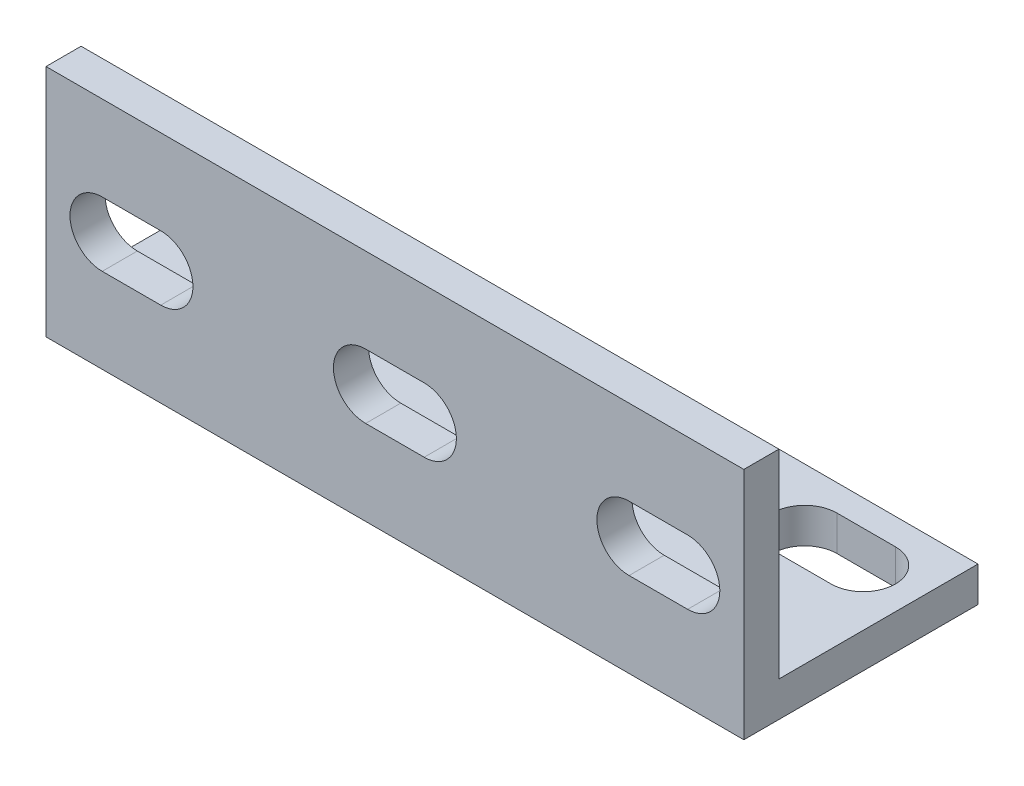
SolidWorks part; units mm, degrees
ref_plane "Front Plane" through (0, 0, 0) normal (0, 0, 1) x (1, 0, 0)
ref_plane "Top Plane" through (0, 0, 0) normal (0, 1, 0) x (1, 0, 0)
ref_plane "Right Plane" through (0, 0, 0) normal (1, 0, 0) x (0, 0, -1)
sketch "Sketch1" plane through (0, 0, 0) normal (1, 0, 0) x (0, 0, -1)
  line L0 (0, 20) -> (0, 0)
  line L1 (0, 0) -> (20, 0)
  line L2 (20, 0) -> (20, 3)
  line L3 (20, 3) -> (3, 3)
  line L4 (3, 3) -> (3, 20)
  line L5 (3, 20) -> (0, 20)
  dimension "D1" = 20
  dimension "D2" = 20
  dimension "D3" = 3
  dimension "D4" = 3
extrude "Boss-Extrude1" add sketch "Sketch1" against normal blind 59.6
sketch "Sketch2" plane through (0, 0, -3) normal (0, 0, -1) x (-1, 0, 0)
  line L0 (29.8, 20) -> (29.8, 3) construction
  line L1 (59.6, 20) -> (0, 20) construction
  line L2 (59.6, 3) -> (0, 3) construction
  line L3 (27.3, 10) -> (32.3, 10) construction
  line L4 (27.3, 12.75) -> (32.3, 12.75)
  line L5 (27.3, 7.25) -> (32.3, 7.25)
  arc A0 (27.3, 12.75) -> (27.3, 7.25) centre (27.3, 10) ccw
  arc A1 (32.3, 7.25) -> (32.3, 12.75) centre (32.3, 10) ccw
  point P8 (29.8, 10)
  dimension "D3" = 7.25
  dimension "D1" = 5.5
  dimension "D2" = 5
extrude "Cut-Extrude1" cut sketch "Sketch2" against normal through all contours L4 A1 L5 A0
pattern_linear "LPattern1" count 2 spacing 22.5 along (-1, 0, 0) count 2 spacing 22.5 along (1, 0, 0) of "Cut-Extrude1"
sketch "Sketch3" plane through (0, 3, 0) normal (0, 1, 0) x (1, 0, 0)
  line L0 (-29.8, 3) -> (-29.8, 20) construction
  line L1 (-59.6, 3) -> (0, 3) construction
  line L2 (-59.6, 20) -> (0, 20) construction
  line L3 (-27.3, 15) -> (-32.3, 15) construction
  line L4 (-27.3, 12.25) -> (-32.3, 12.25)
  line L5 (-27.3, 17.75) -> (-32.3, 17.75)
  arc A0 (-27.3, 12.25) -> (-27.3, 17.75) centre (-27.3, 15) ccw
  arc A1 (-32.3, 17.75) -> (-32.3, 12.25) centre (-32.3, 15) ccw
  point P8 (-29.8, 15)
  dimension "D1" = 5.5
  dimension "D2" = 5
  dimension "D3" = 2.25
extrude "Cut-Extrude2" cut sketch "Sketch3" against normal through all
pattern_linear "LPattern2" count 2 spacing 22.5 along (-1, 0, 0) count 2 spacing 22.5 along (1, 0, 0) of "Cut-Extrude2"
